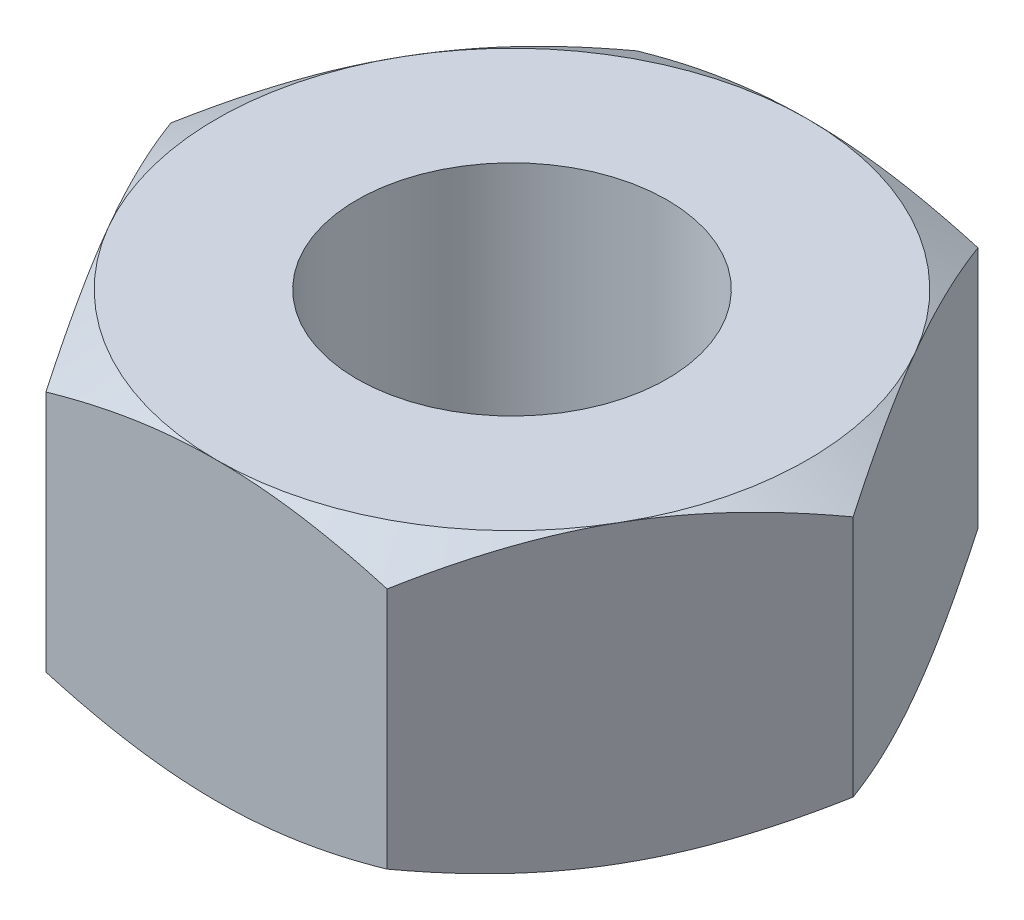
SolidWorks part; units mm, degrees
ref_plane "Front Plane" through (0, 0, 0) normal (0, 0, 1) x (1, 0, 0)
ref_plane "Top Plane" through (0, 0, 0) normal (0, 1, 0) x (1, 0, 0)
ref_plane "Right Plane" through (0, 0, 0) normal (1, 0, 0) x (0, 0, -1)
sketch "Sketch1" plane through (0, 0, 0) normal (0, 1, 0) x (1, 0, 0)
  line L1 (-2.3094, -4) -> (2.3094, -4)
  line L2 (2.3094, -4) -> (4.6188, 0)
  line L3 (4.6188, 0) -> (2.3094, 4)
  line L4 (2.3094, 4) -> (-2.3094, 4)
  line L5 (-2.3094, 4) -> (-4.6188, 0)
  line L6 (-4.6188, 0) -> (-2.3094, -4)
  circle A0 centre (0, 0) radius 4 construction
  dimension "D1" = 8
extrude "Boss-Extrude1" add sketch "Sketch1" along normal blind 4
sketch "Sketch2" plane through (0, 0, 0) normal (1, 0, 0) x (0, 0, -1)
  line L0 (0, 0) -> (0, 3.5465) construction
  line L1 (5.7522, 1.0117) -> (4, 0)
  line L2 (4, 4) -> (6.1161, 4)
  line L5 (6.1161, 4) -> (6.1161, 2.7783)
  line L6 (4, 0) -> (5.7522, 0)
  line L9 (5.7522, 0) -> (5.7522, 1.0117)
  line L10 (6.1161, 2.7783) -> (4, 4)
  dimension "D1" = 30
  dimension "D2" = 30
revolve "Cut-Revolve1" cut sketch "Sketch2" angle 360 about L0
hole_wizard "M5 Tapped Hole1" positions "3DSketch2" profile "Sketch3" tap size "M5" standard "DIN" end condition through all
sketch3d "3DSketch2"
  point P0 (0, 4, 0)
sketch "Sketch3" plane through (0, 4, 0) normal (1, 0, 0) x (0, 0, 1)
  line L0 (0, 0) -> (0, 4)
  line L1 (0, 4) -> (2.1, 4)
  line L2 (2.1, 4) -> (2.1, 0)
  line L5 (2.1, 0) -> (0, 0)
  line L11 (0, -6.35) -> (0, 107.95) construction
  dimension "Thru Tap Drill Dia." = 4.2
  dimension "Thru Tap Drill Depth" = 4
cosmetic thread "Hole Thread1" parameters "D2"=5
